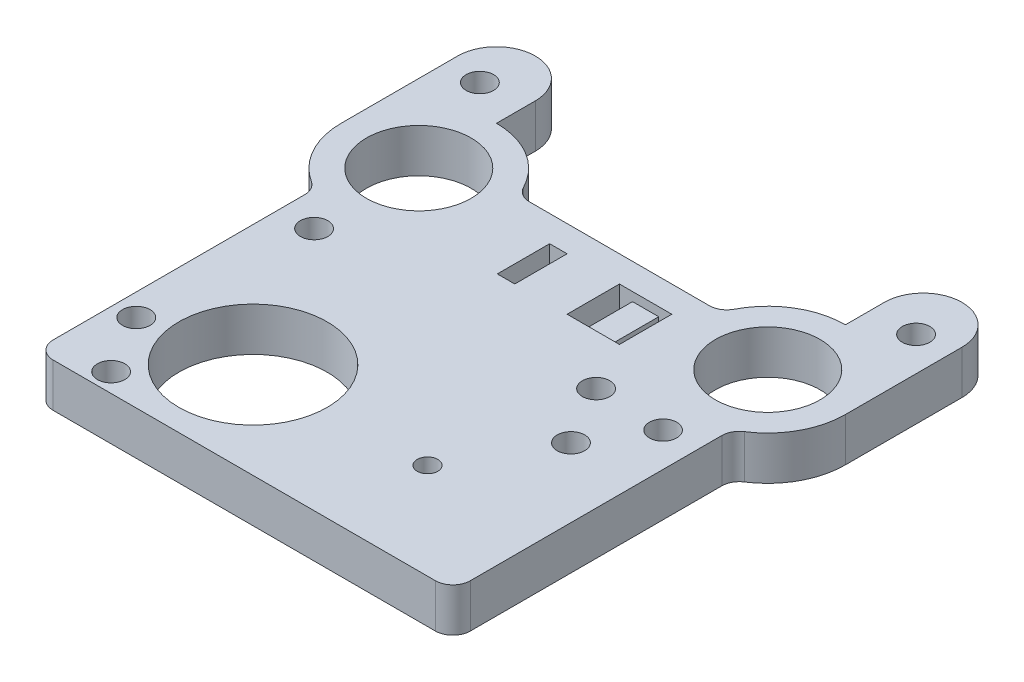
SolidWorks part; units mm, degrees
ref_plane "Front Plane" through (0, 0, 0) normal (0, 0, 1) x (1, 0, 0)
ref_plane "Top Plane" through (0, 0, 0) normal (0, 1, 0) x (1, 0, 0)
ref_plane "Right Plane" through (0, 0, 0) normal (1, 0, 0) x (0, 0, -1)
sketch "Sketch3" plane through (0, 0, 0) normal (0, 1, 0) x (1, 0, 0)
  line L0 (-25.4, 0) -> (25.4, 0) construction
  line L1 (-16.4615, -50.8) -> (-27.82, -50.8)
  line L3 (-13.0915, 3.81) -> (13.0915, 3.81)
  line L4 (4.0008, -50.8) -> (23.2974, -50.8)
  line L6 (27.82, -50.8) -> (23.2974, -50.8)
  line L7 (4.0008, -50.8) -> (-16.4615, -50.8)
  line L8 (-30.36, -48.26) -> (-30.36, -11.6436)
  line L9 (30.36, -48.26) -> (30.36, -11.6436)
  line L10 (-36.71, 16.965) -> (-36.71, 0)
  line L11 (-25.4, 16.965) -> (-25.4, 11.31)
  line L12 (25.4, 16.965) -> (25.4, 11.31)
  line L13 (36.71, 0) -> (36.71, 16.965)
  arc A0 (-15.3488, 5.1855) -> (-25.4, 11.31) centre (-25.4, 0) ccw
  arc A1 (31.5245, -9.5082) -> (36.71, 0) centre (25.4, 0) ccw
  arc A2 (-30.36, -11.6436) -> (-31.5245, -9.5082) centre (-32.9, -11.6436) ccw
  arc A3 (31.5245, -9.5082) -> (30.36, -11.6436) centre (32.9, -11.6436) ccw
  arc A4 (27.82, -50.8) -> (30.36, -48.26) centre (27.82, -48.26) ccw
  arc A5 (-15.3488, 5.1855) -> (-13.0915, 3.81) centre (-13.0915, 6.35) ccw
  arc A6 (15.3488, 5.1855) -> (13.0915, 3.81) centre (13.0915, 6.35) cw
  arc A7 (-27.82, -50.8) -> (-30.36, -48.26) centre (-27.82, -48.26) cw
  arc A8 (-25.4, 16.965) -> (-36.71, 16.965) centre (-31.055, 16.965) ccw
  arc A9 (36.71, 16.965) -> (25.4, 16.965) centre (31.055, 16.965) ccw
  arc A10 (-14.09, 0) -> (-25.4, 11.31) centre (-25.4, 0) ccw
  arc A11 (-36.71, 0) -> (-31.5245, -9.5082) centre (-25.4, 0) ccw
  arc A12 (-36.71, 0) -> (-31.5245, -9.5082) centre (-25.4, 0) ccw
  arc A13 (25.4, 11.31) -> (15.3488, 5.1855) centre (25.4, 0) ccw
  point P2 (0, 0)
  point P3 (0.4374, -2.2293)
  point P10 (-5.9126, -2.2293)
  point P20 (6.7874, -2.2293)
  point P28 (25.4, -11.31)
  point P29 (-25.4, 0)
  point P30 (25.4, 0)
  dimension "D3" = 22.62
  dimension "D4" = 22.62
  dimension "D5" = 3.81
  dimension "D7" = 2.54
  dimension "D8" = 2.54
  dimension "D9" = 2.54
  dimension "D13" = 2.54
  dimension "D14" = 2.54
  dimension "D6" = 2.54
  dimension "D2" = 50.8
  dimension "D11" = 0
  dimension "D12" = 0
extrude "Boss-Extrude2" add sketch "Sketch3" along normal blind 6.35
sketch "Sketch6" plane through (0, 6.35, 0) normal (0, 1, 0) x (1, 0, 0)
  line L1 (-6.35, 0) -> (-3.81, 0)
  line L2 (-6.35, 0) -> (-6.35, -7.62)
  line L3 (-6.35, -7.62) -> (-3.81, -7.62)
  line L4 (-3.81, 0) -> (-3.81, -7.62)
  line L5 (3.81, 0) -> (5.715, 0)
  line L6 (3.81, 0) -> (3.81, -7.62)
  line L7 (3.81, -7.62) -> (5.715, -7.62)
  line L8 (5.715, 0) -> (5.715, -7.62)
  line L9 (9.525, 0) -> (11.43, 0)
  line L10 (9.525, 0) -> (9.525, -7.62)
  line L11 (9.525, -7.62) -> (11.43, -7.62)
  line L12 (11.43, 0) -> (11.43, -7.62)
  dimension "D1" = 2.54
  dimension "D2" = 7.62
  dimension "D3" = 3.81
  dimension "D4" = 3.81
  dimension "D5" = 1.905
  dimension "D6" = 3.81
  dimension "D7" = 1.905
extrude "Cut-Extrude3" cut sketch "Sketch6" against normal blind 6.35
sketch "Sketch7" plane through (0, 6.35, 0) normal (0, 1, 0) x (1, 0, 0)
  circle A0 centre (-12.7, -36.83) radius 10.795
  circle A1 centre (12.7, -36.83) radius 1.5
  dimension "D2" = 36.83
  dimension "D4" = 3
  dimension "D5" = 21.59
  dimension "D1" = 12.7
  dimension "D3" = 12.7
  dimension "D6" = 36.83
extrude "Cut-Extrude4" cut sketch "Sketch7" against normal blind 6.35
sketch "Sketch8" plane through (0, 6.35, 0) normal (0, 1, 0) x (1, 0, 0)
  circle A0 centre (-31.75, 15.24) radius 2
  circle A1 centre (-25.4, -15.24) radius 2
  circle A2 centre (25.4, -15.24) radius 1.9894
  circle A3 centre (31.75, 15.24) radius 2
  point P11 (31.055, 16.965)
  dimension "D1" = 4
  dimension "D3" = 25.4
  dimension "D4" = 4
  dimension "D6" = 4
  dimension "D9" = 15.24
  dimension "D2" = 50.8
  dimension "D5" = 15.24
  dimension "D7" = 15.24
  dimension "D8" = 15.24
  dimension "D10" = 63.5
  dimension "D11" = 31.75
sketch "Sketch10" plane through (0, 6.35, 0) normal (0, 1, 0) x (1, 0, 0)
  circle A0 centre (-25.4, 0) radius 7.62
  circle A1 centre (25.4, 0) radius 7.62
  dimension "D1" = 15.24
  dimension "D2" = 15.24
extrude "Cut-Extrude6" cut sketch "Sketch10" against normal blind 6.35
sketch "Sketch11" plane through (0, 6.35, 0) normal (0, 1, 0) x (1, 0, 0)
  line L0 (5.715, 0) -> (3.81, 0) construction
  line L1 (5.715, 0) -> (9.525, 0)
  line L2 (5.715, 0) -> (5.715, -7.62)
  line L3 (5.715, -7.62) -> (9.525, -7.62)
  line L4 (9.525, 0) -> (9.525, -7.62)
  line L5 (5.715, -7.62) -> (5.715, 0) construction
extrude "Cut-Extrude7" cut sketch "Sketch11" against normal blind 1.27
extrude "Cut-Extrude8" cut sketch "Sketch8" against normal blind 6.35
sketch "Sketch12" plane through (0, 6.35, 0) normal (0, 1, 0) x (1, 0, 0)
  line L0 (-12.7, -36.83) -> (15.7487, -20.4051) construction
  line L1 (-12.7, -36.83) -> (2.6515, -36.83) construction
  line L2 (-22.1338, -48.0501) -> (20.3014, -23.5501) construction
  line L3 (-22.1338, -48.0501) -> (-27.1338, -39.3899) construction
  line L4 (20.3014, -23.5501) -> (15.3014, -14.8899) construction
  line L5 (-27.1338, -39.3899) -> (15.3014, -14.8899) construction
  line L6 (-22.1338, -48.0501) -> (15.3014, -14.8899) construction
  line L7 (20.3014, -23.5501) -> (-27.1338, -39.3899) construction
  circle A0 centre (15.3014, -14.8899) radius 2
  circle A1 centre (20.3014, -23.5501) radius 2
  circle A2 centre (-22.1338, -48.0501) radius 2
  circle A3 centre (-27.1338, -39.3899) radius 2
  point P5 (-3.4162, -31.47)
  dimension "D5" = 4
  dimension "D1" = 30
  dimension "D2" = 49
  dimension "D3" = 10
  dimension "D4" = 0
  dimension "D8" = 13.78
  dimension "D6" = 2
  dimension "D7" = 2
extrude "Cut-Extrude9" cut sketch "Sketch12" against normal blind 6.35
